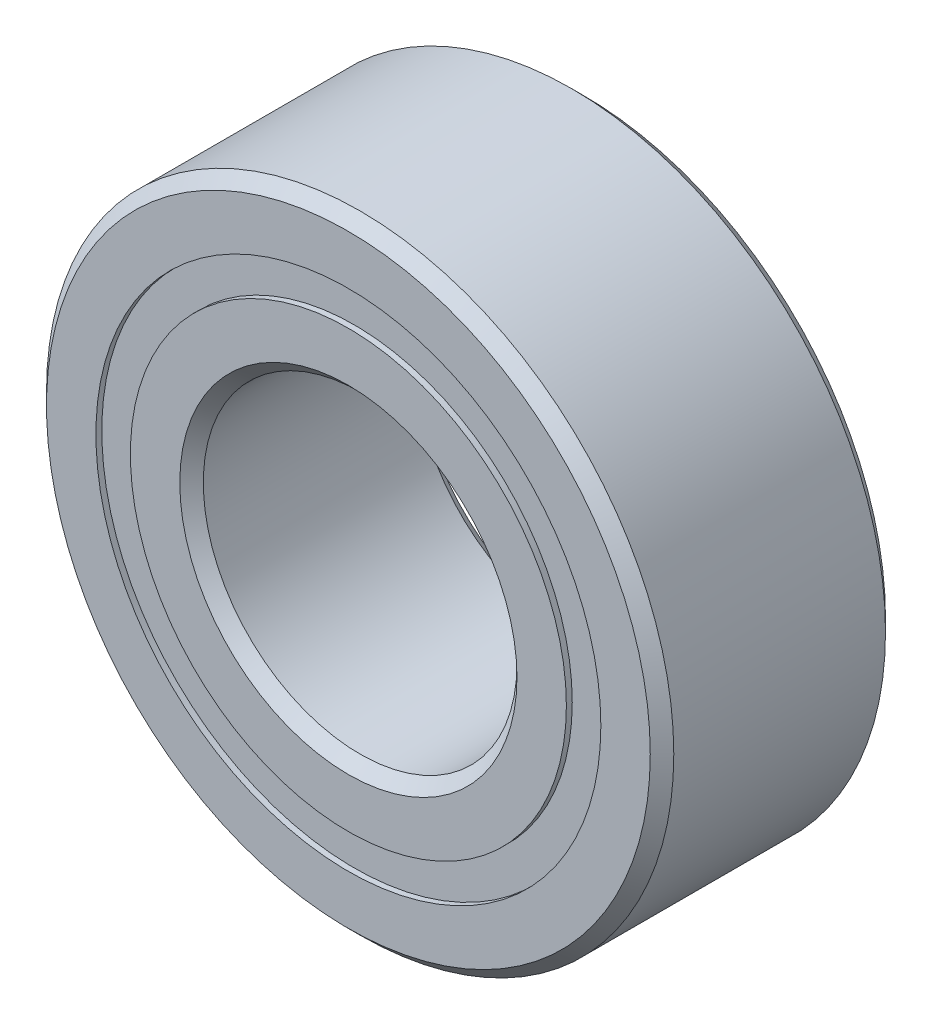
SolidWorks part; units mm, degrees
ref_plane "Front Plane" through (0, 0, 0) normal (0, 0, 1) x (1, 0, 0)
ref_plane "Top Plane" through (0, 0, 0) normal (0, 1, 0) x (1, 0, 0)
ref_plane "Right Plane" through (0, 0, 0) normal (1, 0, 0) x (0, 0, -1)
sketch "Sketch1" plane through (0, 0, 0) normal (0, 1, 0) x (1, 0, 0)
  line L0 (6.35, -2.1431) -> (6.35, 2.1431)
  line L1 (6.35, 2.1431) -> (6.1119, 2.3813)
  line L2 (6.1119, 2.3813) -> (5.1114, 2.3813)
  line L3 (5.1114, 2.3813) -> (5.1114, 2.2622)
  line L4 (5.1114, 2.2622) -> (4.4136, 2.2622)
  line L5 (4.4136, 2.2622) -> (4.4136, 2.3813)
  line L6 (4.4136, 2.3813) -> (3.4131, 2.3813)
  line L7 (3.4131, 2.3813) -> (3.175, 2.1431)
  line L8 (3.175, 2.1431) -> (3.175, -2.1431)
  line L9 (3.175, -2.1431) -> (3.4131, -2.3813)
  line L10 (3.4131, -2.3813) -> (4.4136, -2.3813)
  line L11 (4.4136, -2.3813) -> (4.4136, -2.2622)
  line L12 (4.4136, -2.2622) -> (5.1114, -2.2622)
  line L13 (5.1114, -2.2622) -> (5.1114, -2.3813)
  line L14 (5.1114, -2.3813) -> (6.1119, -2.3813)
  line L15 (6.1119, -2.3813) -> (6.35, -2.1431)
  line L16 (0, 2.3813) -> (0, -2.3813) construction
  point P18 (0, 0)
  dimension "D1" = 3.175
  dimension "D2" = 3.4131
  dimension "D3" = 4.4136
  dimension "D4" = 5.1114
  dimension "D5" = 6.1119
  dimension "D6" = 6.35
  dimension "D7" = 0.1191
  dimension "D8" = 0.2381
  dimension "D9" = 4.5244
  dimension "D10" = 4.6434
  dimension "D11" = 4.7625
revolve "Revolve1" add sketch "Sketch1" angle 360 about L16
